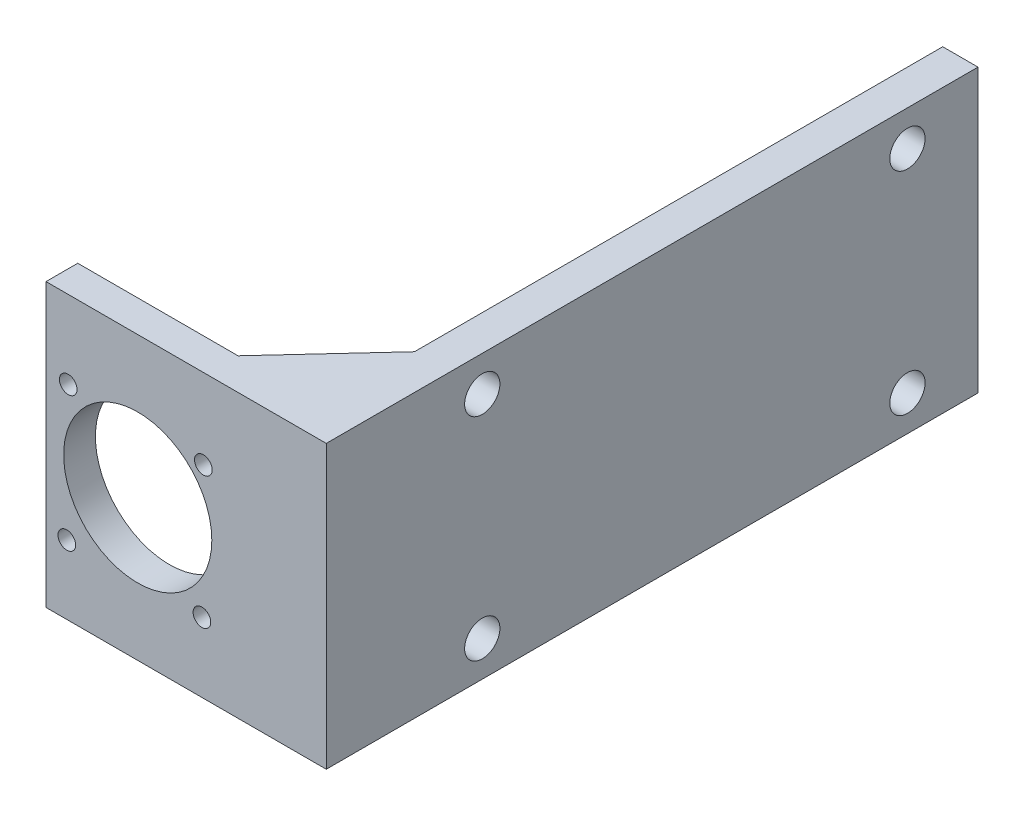
SolidWorks part; units mm, degrees
ref_plane "Front Plane" through (0, 0, 0) normal (0, 0, 1) x (1, 0, 0)
ref_plane "Top Plane" through (0, 0, 0) normal (0, 1, 0) x (1, 0, 0)
ref_plane "Right Plane" through (0, 0, 0) normal (1, 0, 0) x (0, 0, -1)
sketch "Sketch1" plane through (0, 0, 0) normal (0, 0, 1) x (1, 0, 0)
  line L0 (-26, 0) -> (0, 0) construction
  line L1 (-26, -6) -> (0, -6)
  line L2 (-26, -6) -> (-26, 34)
  line L3 (-26, 34) -> (0, 34)
  line L5 (-26, 28) -> (0, 28) construction
  line L6 (0, 34) -> (13.72, 34)
  line L7 (13.72, -36) -> (13.72, 64) construction
  line L8 (0, -6) -> (13.72, -6)
  line L9 (13.72, -6) -> (13.72, 34)
  circle A0 centre (-13, 14) radius 10.5
  circle A1 centre (-3.9, 3.85) radius 1.25
  circle A2 centre (-23.05, 3.75) radius 1.25
  circle A3 centre (-22.85, 22.95) radius 1.25
  circle A4 centre (-3.7, 22.65) radius 1.25
  dimension "D3" = 21
  dimension "D1" = 6
  dimension "D2" = 6
extrude "Boss-Extrude1" add sketch "Sketch1" along normal blind 4.5
sketch "Sketch2" plane through (0, 0, 0) normal (0, 0, -1) x (-1, 0, 0)
  line L0 (26, -6) -> (-13.72, -6) construction
  line L1 (-13.72, 34) -> (-8.72, 34)
  line L2 (-13.72, 34) -> (-13.72, -6)
  line L3 (-13.72, -6) -> (-8.72, -6)
  line L4 (-8.72, 34) -> (-8.72, -6)
  dimension "D1" = 5
extrude "Boss-Extrude2" add sketch "Sketch2" along normal up to surface (87.8698 mm away)
sketch "Sketch3" plane through (8.72, 0, 0) normal (-1, 0, 0) x (0, 0, 1)
  circle A0 centre (-77.8698, 29) radius 2.5
  circle A1 centre (-77.8698, -1) radius 2.5
  circle A2 centre (-17.6098, -1) radius 2.5
  circle A3 centre (-17.6098, 29) radius 2.5
extrude "Cut-Extrude1" cut sketch "Sketch3" against normal through all
ref_plane "Plane1" through (0, 14, 0) normal (0, 1, 0) x (1, 0, 0)
sketch "Sketch4" plane through (0, 14, 0) normal (0, 1, 0) x (1, 0, 0)
  line L0 (8.72, 13) -> (-3.28, 0)
  line L1 (8.72, 87.8698) -> (8.72, 0) construction
  line L2 (8.72, 0) -> (-26, 0) construction
  line L3 (-3.28, 0) -> (8.72, 0)
  line L4 (8.72, 0) -> (8.72, 13)
  dimension "D1" = 12
  dimension "D2" = 13
extrude "Boss-Extrude3" add sketch "Sketch4" along normal mid plane 40
sketch "Sketch5" plane through (0, 0, 0) normal (0, 0, -1) x (-1, 0, 0)
  line L12 (-8.72, 34) -> (-8.72, -6) construction
  line L17 (-8.72, -3) -> (3.28, -3)
  line L18 (-8.72, -3) -> (-8.72, 31)
  line L19 (-8.72, 31) -> (3.28, 31)
  line L20 (3.28, -3) -> (3.28, 31)
  line L21 (3.28, 34) -> (3.28, 23.8273) construction
  line L22 (-8.72, -6) -> (3.28, -6) construction
  line L23 (-8.72, 34) -> (3.28, 34) construction
  dimension "D1" = 3
  dimension "D2" = 3
extrude "Cut-Extrude2" cut sketch "Sketch5" along normal up to vertex (87.8698 mm away)
fillet "Fillet1" radius 5 1 edges at (8.72, 14, 0)
